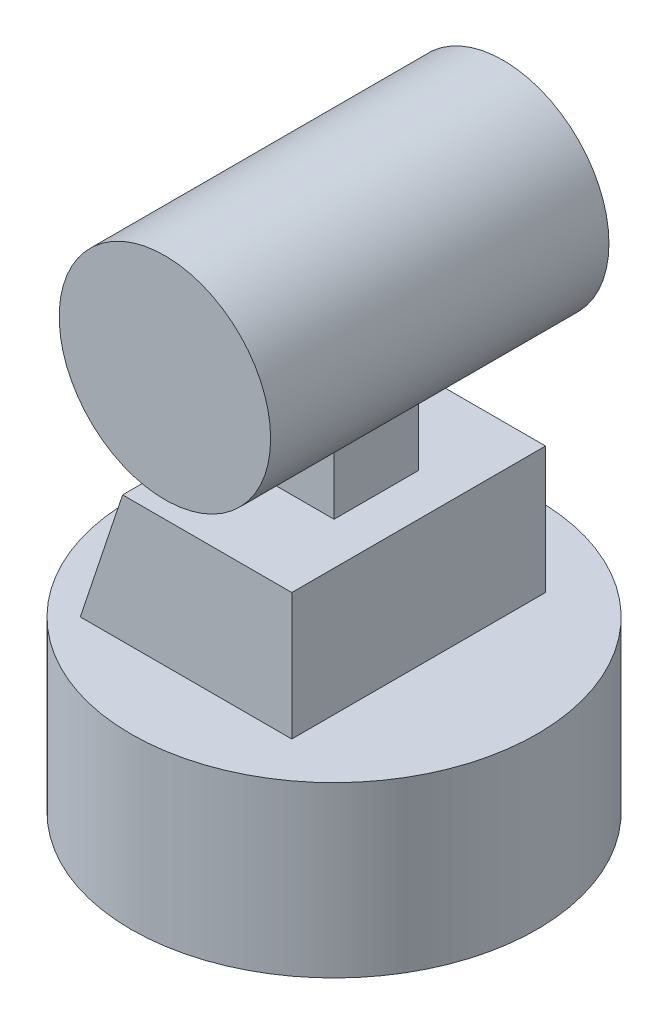
SolidWorks part; units mm, degrees
ref_plane "Front Plane" through (0, 0, 0) normal (0, 0, 1) x (1, 0, 0)
ref_plane "Top Plane" through (0, 0, 0) normal (0, 1, 0) x (1, 0, 0)
ref_plane "Right Plane" through (0, 0, 0) normal (1, 0, 0) x (0, 0, -1)
sketch "Sketch1" plane through (0, 0, 0) normal (0, 1, 0) x (1, 0, 0)
  circle A0 centre (0, 0) radius 24
  dimension "D1" = 48
extrude "Boss-Extrude1" add sketch "Sketch1" along normal blind 20
sketch "Sketch4" plane through (0, 0, 0) normal (0, 0, 1) x (1, 0, 0)
  circle A0 centre (0, 54.5) radius 12.5
  dimension "D1" = 25
  dimension "D2" = 54.5
extrude "Boss-Extrude3" add sketch "Sketch4" along normal mid plane 40 separate body
sketch "Sketch5" plane through (0, 0, 0) normal (0, 0, 1) x (1, 0, 0)
  line L0 (24, 20) -> (-24, 20) construction
  line L1 (-15, 20) -> (10, 20)
  line L2 (-15, 20) -> (-10, 35)
  line L3 (-10, 35) -> (10, 35)
  line L4 (10, 20) -> (10, 35)
  point P6 (0, 35)
  dimension "D1" = 20
  dimension "D2" = 15
  dimension "D3" = 5
extrude "Boss-Extrude5" add sketch "Sketch5" along normal mid plane 30
sketch "Sketch6" plane through (0, 35, 0) normal (0, 1, 0) x (1, 0, 0)
  line L0 (-5, -5) -> (5, 5) construction
  line L1 (-5, 5) -> (5, 5)
  line L2 (-5, 5) -> (-5, -5)
  line L3 (-5, -5) -> (5, -5)
  line L4 (5, 5) -> (5, -5)
  point P4 (0, 0)
  dimension "D1" = 10
extrude "Boss-Extrude6" add sketch "Sketch6" along normal up to surface (8.0436 mm away)
